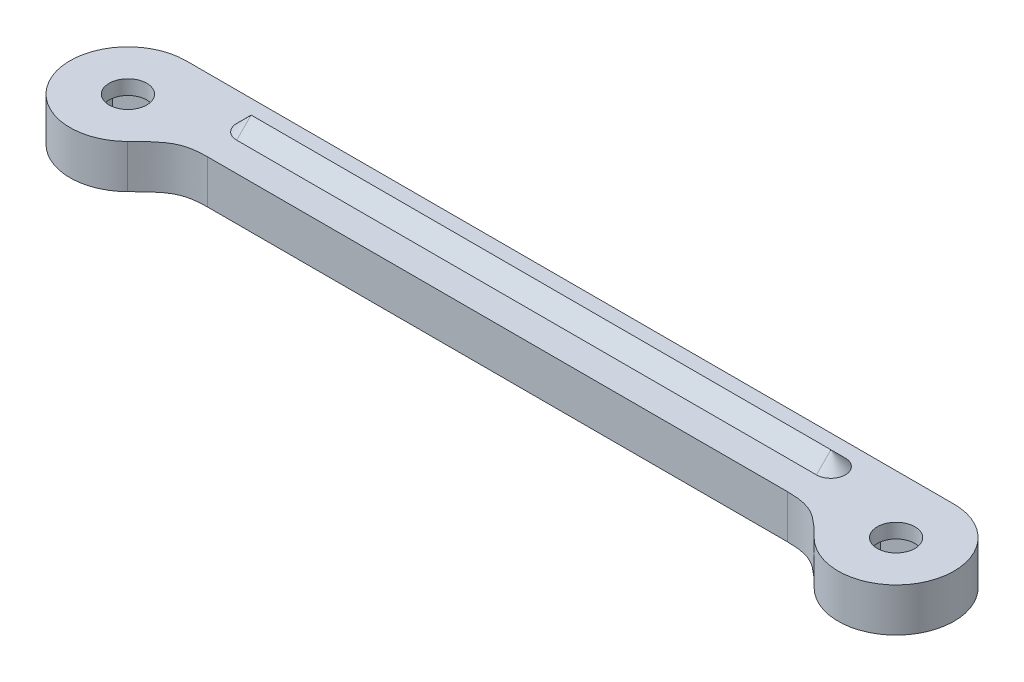
SolidWorks part; units mm, degrees
ref_plane "Front Plane" through (0, 0, 0) normal (0, 0, 1) x (1, 0, 0)
ref_plane "Top Plane" through (0, 0, 0) normal (0, 1, 0) x (1, 0, 0)
ref_plane "Right Plane" through (0, 0, 0) normal (1, 0, 0) x (0, 0, -1)
sketch "Sketch1" plane through (0, 0, 0) normal (0, 1, 0) x (1, 0, 0)
  line L0 (-20, 0) -> (20, 0) construction
  line L1 (0, 1) -> (20, 1) construction
  line L2 (-20, -1) -> (20, -1)
  line L3 (-26.5, 0) -> (26.5, 0) construction
  line L8 (0, -1000) -> (0, 49000) construction
  line L9 (-26.5, 4) -> (26.5, 4)
  line L10 (-20, 1) -> (0, 1) construction
  arc A0 (-20, 1) -> (-21, 0) centre (-20, 0) ccw construction
  arc A1 (20, -1) -> (21, 0) centre (20, 0) ccw construction
  circle A2 centre (-26.5, 0) radius 1.3
  arc A4 (-26.5, 4) -> (-23.679, -2.8359) centre (-26.5, 0) ccw
  circle A5 centre (26.5, 0) radius 1.3
  arc A6 (26.5, 4) -> (23.679, -2.8359) centre (26.5, 0) cw
  arc A7 (-22.5, 0) -> (-26.5, 4) centre (-26.5, 0) ccw construction
  arc A8 (-23.679, -2.8359) -> (-22.5, 0) centre (-26.5, 0) ccw construction
  arc A9 (22.5, 0) -> (26.5, 4) centre (26.5, 0) cw construction
  arc A10 (23.679, -2.8359) -> (22.5, 0) centre (26.5, 0) cw construction
  arc A11 (-21, 0) -> (-20, -1) centre (-20, 0) ccw construction
  arc A12 (21, 0) -> (20, 1) centre (20, 0) ccw construction
  spline S0 degree 3 poles (-20, -1) (-21.1479, -1) (-22.2025, -1.3947) (-23.0935, -2.2534) (-23.679, -2.8359) knots 0 0 0 0 0.551926 1 1 1 1
  spline S1 degree 3 poles (20, -1) (21.1479, -1) (22.2025, -1.3947) (23.0935, -2.2534) (23.679, -2.8359) knots 0 0 0 0 0.551926 1 1 1 1
  point P2 (0, 0)
  point P4 (0, 0)
  point P13 (0, 0)
  point P18 (0, 0)
  dimension "D2" = 1
  dimension "D4" = 2.6
  dimension "D5" = 8
  dimension "D1" = 40
  dimension "D3" = 53
sketch "Sketch2" plane through (0, 0, 0) normal (0, 1, 0) x (1, 0, 0)
  line L0 (-20, 2) -> (20, 2) construction
  line L1 (-20, 3) -> (20, 3)
  line L2 (-20, 1) -> (20, 1)
  line L3 (0, -201000) -> (0, 249000) construction
  line L5 (-26.5, 4) -> (26.5, 4) construction
  arc A0 (-20, 3) -> (-20, 1) centre (-20, 2) ccw
  arc A1 (20, 1) -> (20, 3) centre (20, 2) ccw
  arc A2 (21, 0) -> (20, 1) centre (20, 0) ccw construction
  point P2 (0, 2)
  point P3 (0, 0)
  point P9 (0, 0)
  point P10 (0, 1.583)
  point P18 (0, 2.6273)
  dimension "D1" = 1
extrude "Boss-Extrude1" add sketch "Sketch1" along normal blind 3
extrude "Boss-Extrude2" add sketch "Sketch2" along normal blind 3 draft 45 from surface at 3 starting at face at (-0.6132, 3, 0.6479)
sketch "Sketch3" plane through (0, 0, 0) normal (0, -1, 0) x (1, 0, 0)
  line L1 (-24, 1.4434) -> (-26.5, 2.8868)
  line L2 (-26.5, 2.8868) -> (-29, 1.4434)
  line L3 (-29, 1.4434) -> (-29, -1.4434)
  line L4 (-29, -1.4434) -> (-26.5, -2.8868)
  line L5 (-26.5, -2.8868) -> (-24, -1.4434)
  line L6 (-24, -1.4434) -> (-24, 1.4434)
  line L7 (29, 1.4434) -> (26.5, 2.8868)
  line L8 (26.5, 2.8868) -> (24, 1.4434)
  line L9 (24, 1.4434) -> (24, -1.4434)
  line L10 (24, -1.4434) -> (26.5, -2.8868)
  line L11 (26.5, -2.8868) -> (29, -1.4434)
  line L12 (29, -1.4434) -> (29, 1.4434)
  circle A0 centre (-26.5, 0) radius 2.5 construction
  circle A1 centre (26.5, 0) radius 2.5 construction
  dimension "D1" = 5
extrude "Cut-Extrude1" cut sketch "Sketch3" against normal blind 2 draft 5 draft outward yes
